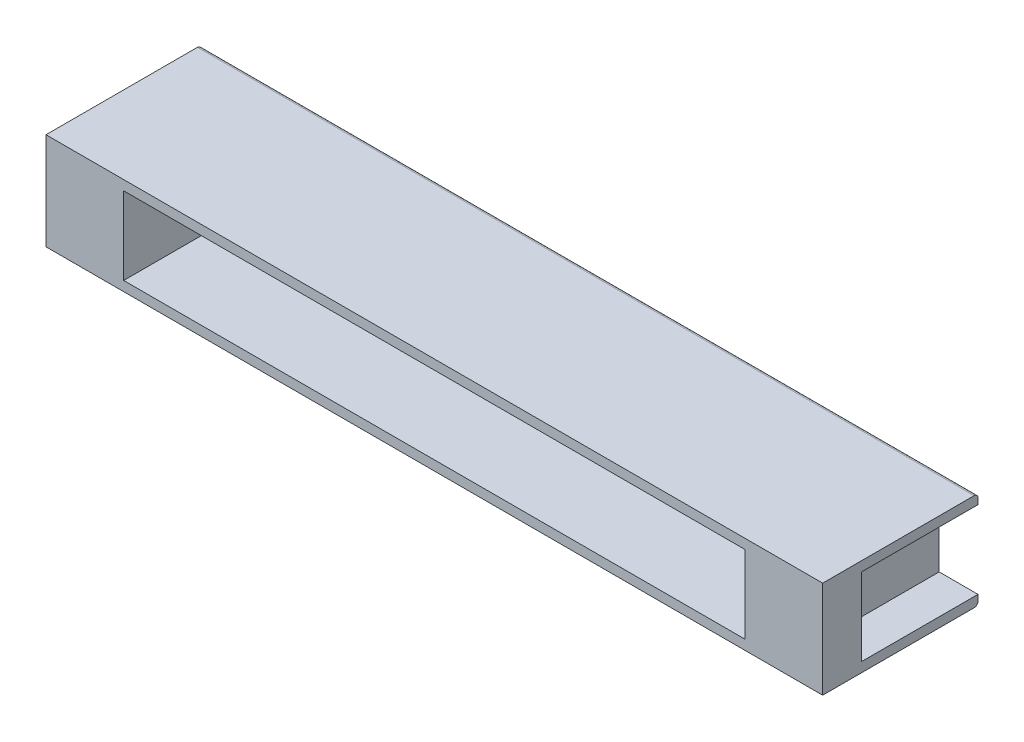
SolidWorks part; units mm, degrees
ref_plane "Front Plane" through (0, 0, 0) normal (0, 0, 1) x (1, 0, 0)
ref_plane "Top Plane" through (0, 0, 0) normal (0, 1, 0) x (1, 0, 0)
ref_plane "Right Plane" through (0, 0, 0) normal (1, 0, 0) x (0, 0, -1)
sketch "Sketch1" plane through (0, 0, 0) normal (0, 0, 1) x (1, 0, 0)
  line L1 (-10, 1.25) -> (10, 1.25)
  line L2 (-10, 1.25) -> (-10, -1.25)
  line L3 (-10, -1.25) -> (10, -1.25)
  line L4 (10, 1.25) -> (10, -1.25)
  line L5 (-10, 1.25) -> (10, -1.25) construction
  line L6 (-10, -1.25) -> (10, 1.25) construction
  point P0 (0, 0)
  dimension "D1" = 20
  dimension "D2" = 2.5
extrude "Boss-Extrude1" add sketch "Sketch1" along normal blind 4
sketch "Sketch2" plane through (0, 0, 4) normal (0, 0, 1) x (1, 0, 0)
  line L0 (-10, 1.25) -> (-10, -1.25) construction
  line L1 (-10, 1) -> (-9, 1)
  line L2 (-10, 1) -> (-10, -1)
  line L3 (-10, -1) -> (-9, -1)
  line L4 (-9, 1) -> (-9, -1)
  line L5 (10, -1.25) -> (10, 1.25) construction
  line L6 (10, -1) -> (9, -1)
  line L7 (10, -1) -> (10, 1)
  line L8 (10, 1) -> (9, 1)
  line L9 (9, -1) -> (9, 1)
  line L10 (10, 1.25) -> (-10, 1.25) construction
  line L11 (-10, -1.25) -> (10, -1.25) construction
  line L13 (-8, 1) -> (8, 1)
  line L14 (-8, 1) -> (-8, -1)
  line L15 (-8, -1) -> (8, -1)
  line L16 (8, 1) -> (8, -1)
  dimension "D1" = 1
  dimension "D2" = 2
  dimension "D3" = 0.25
  dimension "D4" = 2
  dimension "D5" = 0.25
  dimension "D6" = 1
  dimension "D7" = 16
  dimension "D8" = 8
  dimension "D9" = 0.25
  dimension "D10" = 0.25
extrude "Cut-Extrude1" cut sketch "Sketch2" against normal blind 4
sketch "Sketch3" plane through (0, 0, 0) normal (0, 0, -1) x (-1, 0, 0)
  line L1 (-8, 1) -> (8, 1)
  line L2 (-8, 1) -> (-8, -1)
  line L3 (-8, -1) -> (8, -1)
  line L4 (8, 1) -> (8, -1)
extrude "Boss-Extrude2" add sketch "Sketch3" against normal blind 1
ref_plane "Plane1" through (6.75, 0, 0) normal (1, 0, 0) x (0, 0, -1)
sketch "Sketch4" plane through (6.75, 0, 0) normal (1, 0, 0) x (0, 0, -1)
  line L0 (0, 0.2302) -> (0.5678, 0.2302)
  line L1 (0, 1) -> (0, -1) construction
  line L2 (0.9926, -0.0062) -> (1.3075, -0.5136)
  line L3 (1.7324, -0.75) -> (1.9, -0.75)
  line L4 (2, -0.85) -> (2, -1.15)
  line L5 (1.9, -1.25) -> (1.4542, -1.25)
  line L6 (1.0294, -1.0136) -> (0.7145, -0.5062)
  line L7 (0.2896, -0.2698) -> (0, -0.2698)
  line L8 (0, -0.2698) -> (0, 0.2302)
  line L9 (-4, -1.25) -> (0, -1.25) construction
  arc A0 (0.5678, 0.2302) -> (0.9926, -0.0062) centre (0.5678, -0.2698) cw
  arc A1 (1.3075, -0.5136) -> (1.7324, -0.75) centre (1.7324, -0.25) ccw
  arc A2 (1.4542, -1.25) -> (1.0294, -1.0136) centre (1.4542, -0.75) cw
  arc A3 (0.7145, -0.5062) -> (0.2896, -0.2698) centre (0.2896, -0.7698) ccw
  arc A4 (2, -1.15) -> (1.9, -1.25) centre (1.9, -1.15) cw
  arc A5 (2, -0.85) -> (1.9, -0.75) centre (1.9, -0.85) ccw
  dimension "D6" = 0.5
  dimension "D7" = 0.1
  dimension "D1" = 2
  dimension "D2" = 0.5
  dimension "D3" = 0.5
  dimension "D4" = 0.5
  dimension "D5" = 0
extrude "Boss-Extrude3" add sketch "Sketch4" along normal blind 0.5
pattern_linear "LPattern1" count 15 spacing 1 along (-1, 0, 0) of "Boss-Extrude3"
sketch "Sketch5" plane through (0, 0, 4) normal (0, 0, 1) x (1, 0, 0)
  line L1 (-10, 1) -> (-9, 1)
  line L2 (-10, 1) -> (-10, -1)
  line L3 (-10, -1) -> (-9, -1)
  line L4 (-9, 1) -> (-9, -1)
  line L5 (10, 1) -> (9, 1)
  line L6 (10, 1) -> (10, -1)
  line L7 (10, -1) -> (9, -1)
  line L8 (9, 1) -> (9, -1)
extrude "Boss-Extrude4" add sketch "Sketch5" against normal blind 1
fillet "Fillet1" radius 0.1 2 edges at (0, -1.25, 0) (0, 1.25, 0)
